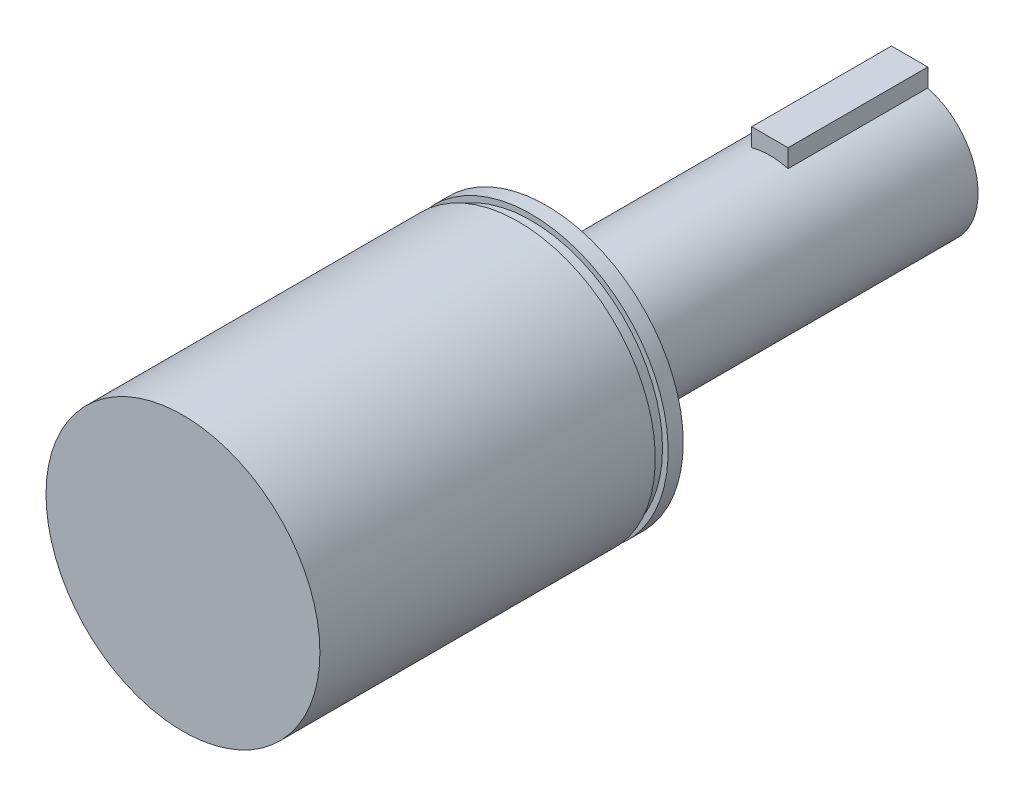
SolidWorks part; units mm, degrees
material "AISI 1020"
ref_plane "Front Plane" through (0, 0, 0) normal (0, 0, 1) x (1, 0, 0)
ref_plane "Top Plane" through (0, 0, 0) normal (0, 1, 0) x (1, 0, 0)
ref_plane "Right Plane" through (0, 0, 0) normal (1, 0, 0) x (0, 0, -1)
sketch "Sketch1" plane through (0, 0, 0) normal (0, 0, 1) x (1, 0, 0)
  circle A0 centre (0, 0) radius 6.223
  dimension "D1" = 12.446
extrude "Boss-Extrude1" add sketch "Sketch1" along normal blind 33.02
sketch "Sketch2" plane through (0, 0, 33.02) normal (0, 0, 1) x (1, 0, 0)
  circle A0 centre (0, 0) radius 12.446
  dimension "D1" = 24.892
extrude "Boss-Extrude2" add sketch "Sketch2" along normal blind 33.02
sketch "Sketch3" plane through (0, 0, 0) normal (0, 0, -1) x (-1, 0, 0)
  line L1 (-1.651, 7.651) -> (1.651, 7.651)
  line L2 (-1.651, 7.651) -> (-1.651, 4.349)
  line L3 (-1.651, 4.349) -> (1.651, 4.349)
  line L4 (1.651, 7.651) -> (1.651, 4.349)
  circle A0 centre (0, 0) radius 6.223 construction
  point P4 (0, 4.349)
  point P6 (-1.651, 6)
  dimension "D1" = 3.302
  dimension "D2" = 3.302
extrude "Boss-Extrude3" add sketch "Sketch3" against normal blind 12.7
ref_plane "Plane1" through (0, 0, 35.56) normal (0, 0, 1) x (1, 0, 0)
sketch "Sketch4" plane through (0, 0, 35.56) normal (0, 0, 1) x (1, 0, 0)
  line L0 (-17.2034, 15.2919) -> (-17.2034, -16.3841)
  line L1 (-17.2034, -16.3841) -> (20.9767, -17.2778)
  line L2 (20.9767, -17.2778) -> (19.7851, 16.682)
  line L3 (19.7851, 16.682) -> (-17.2034, 15.2919)
  circle A0 centre (0, 0) radius 11.938
  dimension "D1" = 23.876
extrude "Cut-Extrude1" cut sketch "Sketch4" against normal blind 1.1684
